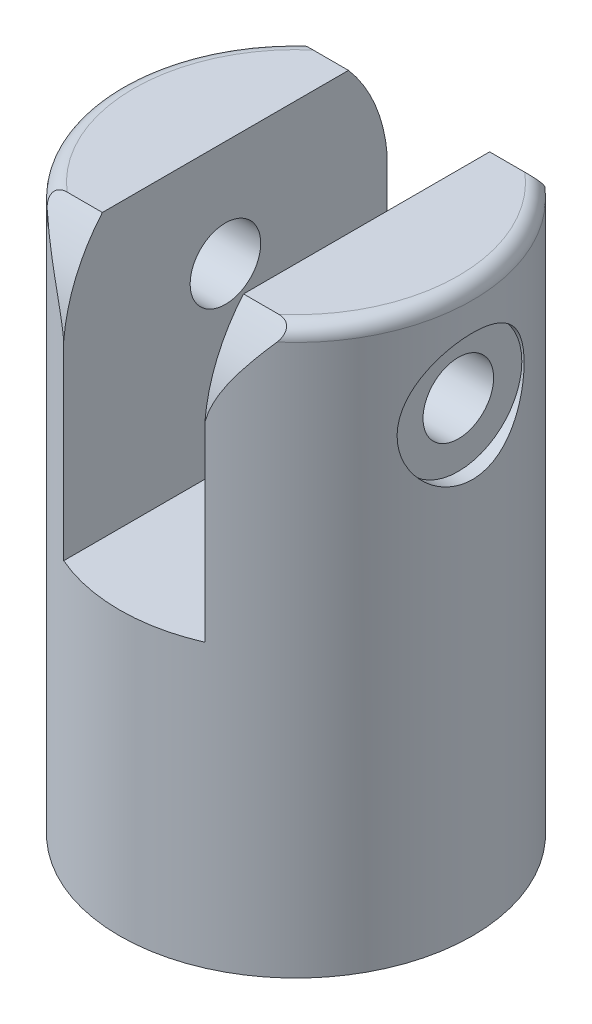
SolidWorks part; units mm, degrees
ref_plane "Front Plane" through (0, 0, 0) normal (0, 0, 1) x (1, 0, 0)
ref_plane "Top Plane" through (0, 0, 0) normal (0, 1, 0) x (1, 0, 0)
ref_plane "Right Plane" through (0, 0, 0) normal (1, 0, 0) x (0, 0, -1)
sketch "Sketch1" plane through (0, 0, 0) normal (0, 1, 0) x (1, 0, 0)
  circle A0 centre (0, 0) radius 125
  dimension "D1" = 250
extrude "Boss-Extrude1" add sketch "Sketch1" along normal blind 400
sketch "Sketch2" plane through (0, 400, 0) normal (0, 1, 0) x (1, 0, 0)
  line L1 (-50, 125) -> (50, 125)
  line L2 (-50, 125) -> (-50, -125)
  line L3 (-50, -125) -> (50, -125)
  line L4 (50, 125) -> (50, -125)
  line L5 (-50, 125) -> (50, -125) construction
  line L6 (-50, -125) -> (50, 125) construction
  circle A0 centre (0, 0) radius 125 construction
  point P0 (0, 0)
  dimension "D1" = 100
extrude "Cut-Extrude1" cut sketch "Sketch2" against normal blind 200
sketch "Sketch3" plane through (-50, 0, 0) normal (1, 0, 0) x (0, 0, -1)
  line L0 (114.5644, 400) -> (-114.5644, 400) construction
  line L1 (114.5644, 200) -> (-114.5644, 200) construction
  line L2 (-114.5644, 200) -> (114.5644, 200)
  line L3 (114.5644, 200) -> (114.5644, 400)
  line L4 (114.5644, 400) -> (-114.5644, 300)
  line L5 (-114.5644, 300) -> (-114.5644, 200)
  circle A0 centre (0, 325) radius 30
  circle A1 centre (0, 200) radius 114.5644
  dimension "D2" = 60
  dimension "D1" = 75
sketch "Sketch4" plane through (0, 0, 0) normal (0, -1, 0) x (1, 0, 0)
  circle A0 centre (0, 0) radius 50
  dimension "D1" = 100
extrude "Cut-Extrude3" cut sketch "Sketch4" against normal blind 60
ref_plane "Plane1" through (-125, 0, 0) normal (1, 0, 0) x (0, 0, -1)
ref_plane "Plane2" through (125, 0, 0) normal (-1, 0, 0) x (0, 0, 1)
sketch "Sketch7" plane through (-50, 0, 0) normal (1, 0, 0) x (0, 0, -1)
  line L0 (114.5644, 400) -> (-114.5644, 400) construction
  line L1 (-115, 325) -> (-114.5644, 400)
  line L2 (-114.5644, 400) -> (114.5644, 400)
  line L3 (114.5644, 400) -> (115, 325)
  circle A0 centre (0, 325) radius 25
  circle A1 centre (0, 325) radius 115
  line M1 (114.5644, 400) -> (-114.5644, 400)
  line M2 (-114.5644, 400) -> (-114.5644, 200)
  line M4 (114.5644, 200) -> (114.5644, 400)
  dimension "D2" = 50
  dimension "D1" = 75
  dimension "D3" = 90
extrude "Cut-Extrude6" cut sketch "Sketch7" against normal through all both and the other way through all contours A1 M1 M2 | A1 M4 M1 | A0
fillet "Fillet2" radius 10 4 edges at (125, 400, 0) (-58.2596, 356.5307, 110.593) (-125, 400, 0) (64.1952, 366.4853, -107.2566)
ref_plane "Plane3" through (-125, 0, 0) normal (1, 0, 0) x (0, 0, -1)
sketch "Sketch8" plane through (-125, 0, 0) normal (1, 0, 0) x (0, 0, -1)
  circle A0 centre (0, 325) radius 45
  circle A1 centre (0, 325) radius 25 construction
  circle A2 centre (0, 325) radius 25
  dimension "D1" = 20
extrude "Cut-Extrude7" cut sketch "Sketch8" along normal blind 10
ref_plane "Plane4" through (125, 0, 0) normal (-1, 0, 0) x (0, 0, 1)
sketch "Sketch10" plane through (125, 0, 0) normal (-1, 0, 0) x (0, 0, 1)
  circle A0 centre (0, 325) radius 45
  circle A1 centre (0, 325) radius 25 construction
  circle A2 centre (0, 325) radius 25
  dimension "D1" = 20
extrude "Cut-Extrude8" cut sketch "Sketch10" along normal blind 10
